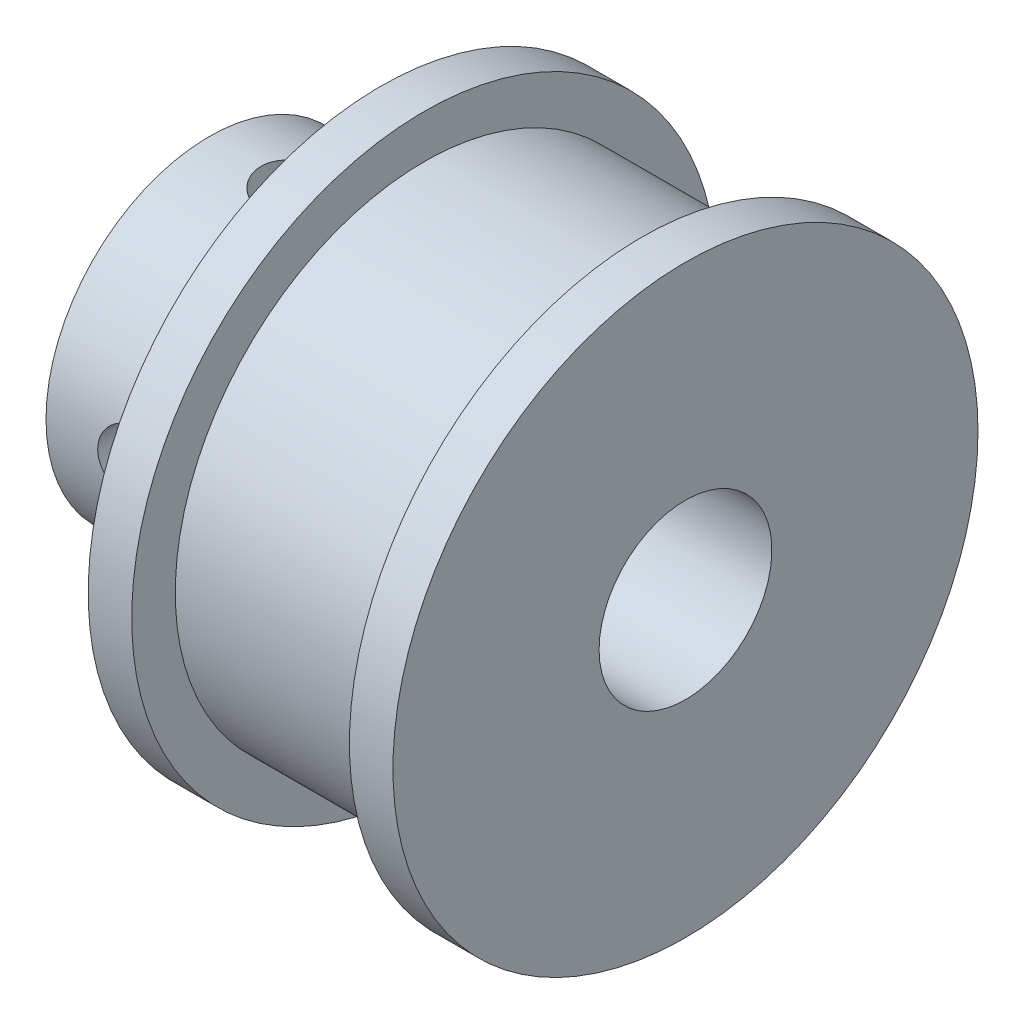
SolidWorks part; units mm, degrees
ref_plane "Front Plane" through (0, 0, 0) normal (0, 0, 1) x (1, 0, 0)
ref_plane "Top Plane" through (0, 0, 0) normal (0, 1, 0) x (1, 0, 0)
ref_plane "Right Plane" through (0, 0, 0) normal (1, 0, 0) x (0, 0, -1)
sketch "Sketch1" plane through (0, 0, 0) normal (0, 0, 1) x (1, 0, 0)
  line L0 (6.3, 10.75) -> (6.3, 0)
  line L1 (6.3, 0) -> (17.5, 0)
  line L2 (17.5, 0) -> (17.5, 10.75)
  line L3 (17.5, 10.75) -> (15.9, 10.75)
  line L4 (15.9, 10.75) -> (15.9, 9.15)
  line L5 (15.9, 9.15) -> (7.9, 9.15)
  line L6 (7.9, 9.15) -> (7.9, 10.75)
  line L7 (7.9, 10.75) -> (6.3, 10.75)
  line L8 (6.3, 0) -> (17.5, 0) construction
revolve "Revolve1" add sketch "Sketch1" angle 360 about L8
sketch "Sketch2" plane through (6.3, 0, 0) normal (-1, 0, 0) x (0, 0, 1)
  circle A0 centre (0, 0) radius 6
extrude "Boss-Extrude1" add sketch "Sketch2" along normal blind 6.3
hole_wizard "Hole1" positions "Sketch4" profile "Sketch3" legacy
sketch "Sketch4" plane through (0, 0, 0) normal (-1, 0, 0) x (0, 0, 1)
  point P0 (0, 0)
sketch "Sketch3" plane through (0, 0, 0) normal (0, 1, 0) x (0, 0, 1)
  line L0 (0, 0) -> (0, 17.5)
  line L1 (0, 17.5) -> (3.175, 17.5)
  line L2 (3.175, 17.5) -> (3.175, 0)
  line L3 (3.175, 0) -> (0, 0)
  line L4 (0, 110) -> (0, -10) construction
  dimension "Diameter" = 6.35
  dimension "Depth" = 17.5
ref_plane "Plane1" through (0, 2.9186, 0) normal (0, -1, 0) x (-1, 0, 0)
hole_wizard "Ø2.5 (2.5) Diameter Hole1" positions "Sketch6" profile "Sketch5" hole size "Ø2.5" standard "ANSI Metric"
sketch "Sketch6" plane through (0, 2.9186, 0) normal (0, -1, 0) x (-1, 0, 0)
  point P0 (-3.15, 0)
sketch "Sketch5" plane through (3.15, 2.9186, 0) normal (1, 0, 0) x (0, 0, -1)
  line L0 (0, 0) -> (0, 7.8314)
  line L1 (0, 7.8314) -> (1.25, 7.8314)
  line L2 (1.25, 7.8314) -> (1.25, 0)
  line L5 (1.25, 0) -> (0, 0)
  line L11 (0, -6.35) -> (0, 107.95) construction
  dimension "Thru Hole Dia." = 2.5
  dimension "Thru Hole Depth" = 7.8314
hole_wizard "Ø2.5 (2.5) Diameter Hole2" positions "3DSketch1" profile "Sketch7" hole size "Ø2.5" standard "ANSI Metric"
sketch3d "3DSketch1"
  point P0 (3.15, 0, 6)
sketch "Sketch7" plane through (3.15, 0, 6) normal (1, 0, 0) x (0, -1, 0)
  line L0 (0, 0) -> (0, 2.825)
  line L1 (0, 2.825) -> (1.25, 2.825)
  line L2 (1.25, 2.825) -> (1.25, 0)
  line L5 (1.25, 0) -> (0, 0)
  line L11 (0, -6.35) -> (0, 107.95) construction
  dimension "Thru Hole Dia." = 2.5
  dimension "Thru Hole Depth" = 2.825
